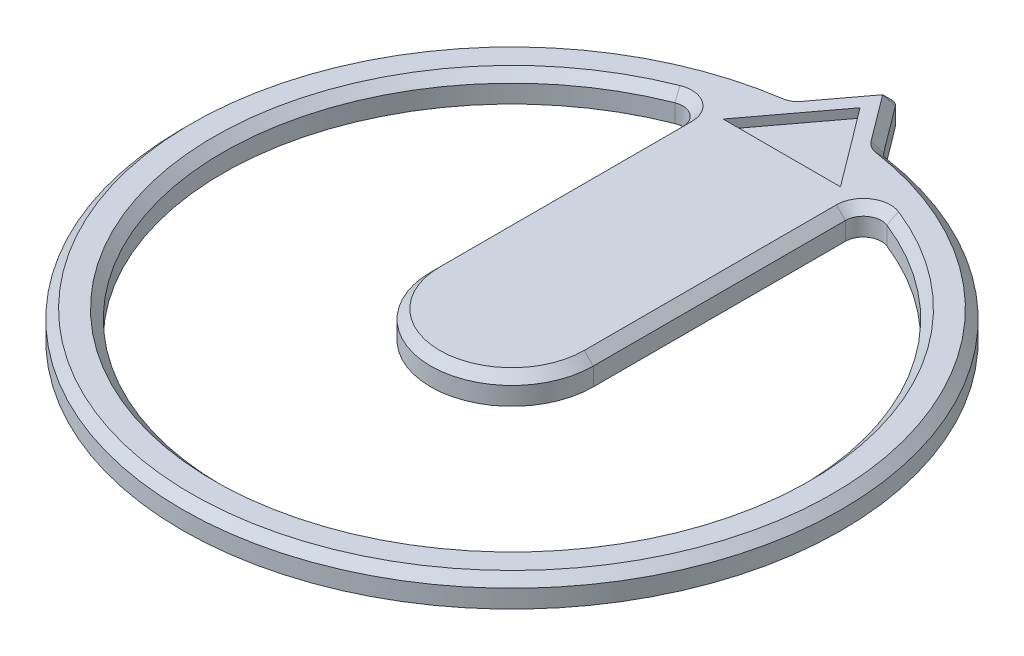
SolidWorks part; units mm, degrees
ref_plane "Front Plane" through (0, 0, 0) normal (0, 0, 1) x (1, 0, 0)
ref_plane "Top Plane" through (0, 0, 0) normal (0, 1, 0) x (1, 0, 0)
ref_plane "Right Plane" through (0, 0, 0) normal (1, 0, 0) x (0, 0, -1)
sketch "Sketch2" plane through (0, 0, 0) normal (0, 1, 0) x (1, 0, 0)
  circle A0 centre (0, 0) radius 5.5
  circle A1 centre (0, 0) radius 3.2
  circle A2 centre (0, 0) radius 0.7862
  dimension "D1" = 11
  dimension "D2" = 2.3
extrude "Boss-Extrude1" add sketch "Sketch2" along normal blind 0.3 contours A2 | A0 A1
sketch "Sketch3" plane through (0, 0.3, 0) normal (0, 1, 0) x (1, 0, 0)
  line L0 (0, 0) -> (0, 3.4415) construction
  line L1 (-0.9, 0) -> (-0.9, 3.4415)
  line L2 (0.9, 0) -> (0.9, 3.4415)
  line L3 (0, 0) -> (0, 3.4415) construction
  line L4 (-0.9, 3.4415) -> (0.9, 3.4415)
  arc A0 (-0.9, 0) -> (0.9, 0) centre (0, 0) ccw
  point P3 (0, 2.0038)
  point P10 (0, 2.0038)
  dimension "D1" = 0.9
extrude "Boss-Extrude2" add sketch "Sketch3" against normal up to surface (0.3 mm away) up to face at (0, 0, 3.2)
sketch "Sketch4" plane through (0, 0.3, 0) normal (0, 1, 0) x (1, 0, 0)
  line L4 (-0.9, 3.0708) -> (0, 4.2708)
  line L5 (0, 4.2708) -> (0.9, 3.0708)
  line L6 (0.9, 3.0708) -> (-0.9, 3.0708) construction
  circle A0 centre (0, 0) radius 3.65
  circle A1 centre (0, 0) radius 5.95
  arc A2 (-0.9, 3.0708) -> (0.9, 3.0708) centre (0, 0) ccw construction
  circle A3 centre (0, 0) radius 5.5 construction
  dimension "D2" = 0.45
  dimension "D3" = 0.45
  dimension "D4" = 1.2
extrude "Cut-Extrude1" cut sketch "Sketch4" against normal through all
fillet "Fillet1" radius 0.2 2 edges at (0.9, 0.15, -3.0708) (-0.9, 0.15, -3.0708)
fillet "Fillet2" radius 0.1 3 edges at (0.4904, 0.15, -3.6169) (-0.4904, 0.15, -3.6169) (0, 0.15, -4.2708)
chamfer "Chamfer1" distance 0.1 angle 45 12 edges at (-0.2728, 0.3, -3.9071) (0.2728, 0.3, -3.9071) (0, 0.3, 3.65) (0, 0.3, 0.9) (-0.9, 0.3, -1.3955) (-0.9875, 0.3, -2.9564) (0, 0.3, 3.2) (0.9875, 0.3, -2.9564) (0.9, 0.3, -1.3955) (0.4944, 0.3, -3.6242) (-0.4944, 0.3, -3.6242) (0, 0.3, -4.2042)
sketch "Sketch5" plane through (0, 0.3, 0) normal (0, 1, 0) x (1, 0, 0)
  line L2 (-0.65, 2.9875) -> (0.65, 2.9875)
  line L3 (-0.8, 2.7911) -> (-0.8, 0) construction
  line L4 (0.2655, 3.5001) -> (0, 3.8542)
  line L5 (0, 3.8542) -> (-0.2655, 3.5001)
  line L6 (0.65, 2.9875) -> (0, 3.8542)
  line L7 (0, 3.8542) -> (-0.65, 2.9875)
  dimension "D2" = 0.15
  dimension "D1" = 0.15
extrude "Cut-Extrude2" cut sketch "Sketch5" against normal blind 0.1
